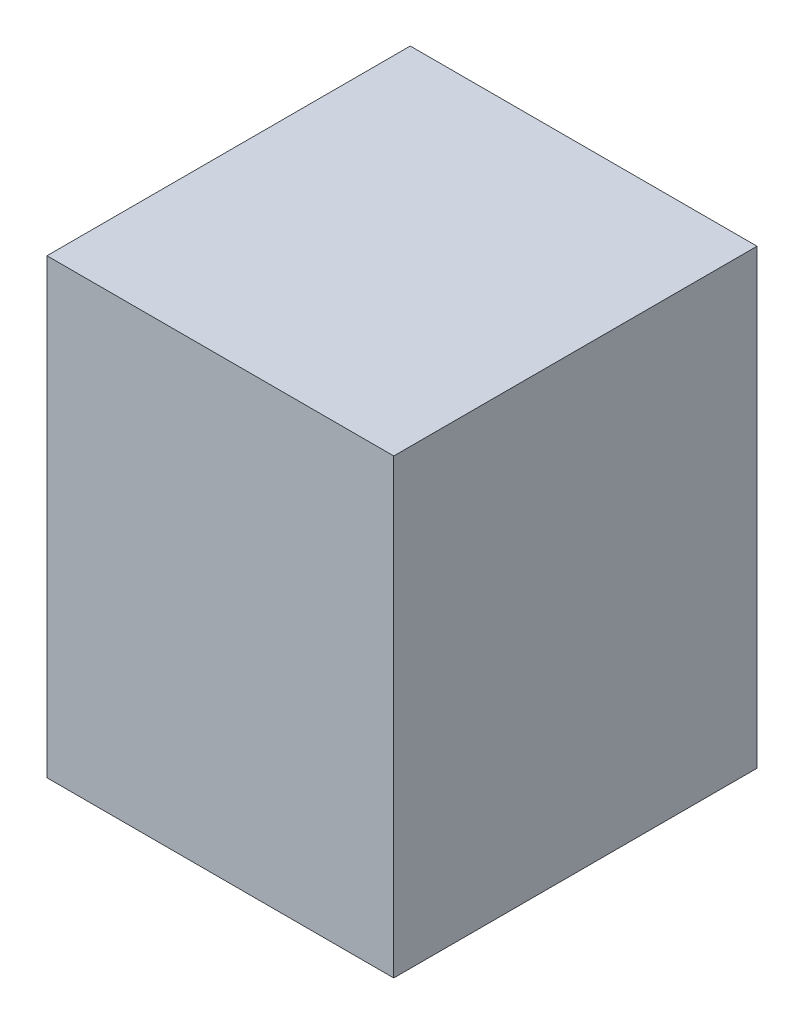
SolidWorks part; units mm, degrees
ref_plane "Front Plane" through (0, 0, 0) normal (0, 0, 1) x (1, 0, 0)
ref_plane "Top Plane" through (0, 0, 0) normal (0, 1, 0) x (1, 0, 0)
ref_plane "Right Plane" through (0, 0, 0) normal (1, 0, 0) x (0, 0, -1)
sketch "Sketch1" plane through (0, 0, 0) normal (0, 0, 1) x (1, 0, 0)
  line L1 (419.1, 552.45) -> (0, 552.45)
  line L2 (419.1, 552.45) -> (419.1, 0)
  line L3 (419.1, 0) -> (0, 0)
  line L4 (0, 552.45) -> (0, 0)
  line L5 (-10, -10) -> (429.1, -10)
  line L6 (-10, -10) -> (-10, 562.45)
  line L7 (-10, 562.45) -> (429.1, 562.45)
  line L8 (429.1, -10) -> (429.1, 562.45)
extrude "Boss-Extrude1" add sketch "Sketch1" along normal blind 450
sketch "Sketch3" plane through (0, 0, 450) normal (0, 0, 1) x (1, 0, 0)
  line L1 (429.1, 562.45) -> (-10, 562.45)
  line L2 (429.1, 562.45) -> (429.1, -10)
  line L3 (429.1, -10) -> (-10, -10)
  line L4 (-10, 562.45) -> (-10, -10)
extrude "Boss-Extrude2" add sketch "Sketch3" along normal blind 10
